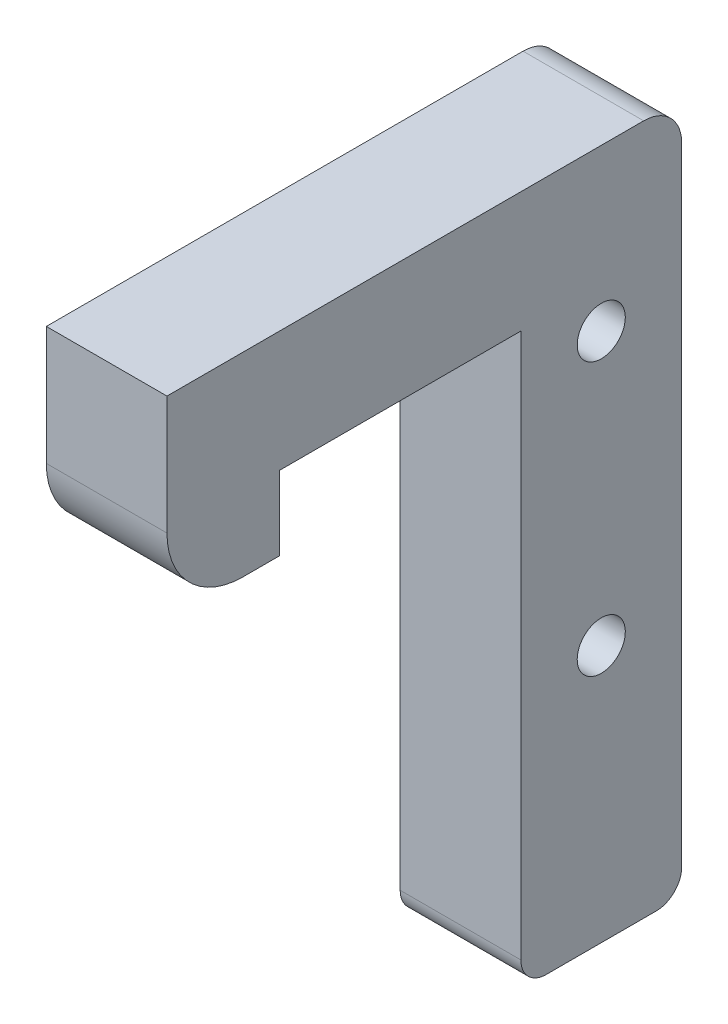
SolidWorks part; units mm, degrees
ref_plane "정면" through (0, 0, 0) normal (0, 0, 1) x (1, 0, 0)
ref_plane "윗면" through (0, 0, 0) normal (0, 1, 0) x (1, 0, 0)
ref_plane "우측면" through (0, 0, 0) normal (1, 0, 0) x (0, 0, -1)
sketch "Sketch1" plane through (0, 0, 0) normal (0, 0, 1) x (1, 0, 0)
  line L1 (0, 0) -> (-9.525, 0)
  line L2 (0, 0) -> (0, 9.525)
  line L3 (0, 9.525) -> (-9.525, 9.525)
  line L4 (-9.525, 0) -> (-9.525, 9.525)
  dimension "D1" = 9.525
  dimension "D2" = 9.525
extrude "Extrude1" add sketch "Sketch1" along normal blind 40.64
ref_plane "Plane1" through (-9.525, 0, 40.64) normal (0, 0, -1) x (-1, 0, 0)
sketch "Sketch3" plane through (0, 0, 0) normal (0, -1, 0) x (1, 0, 0)
  line L0 (0, 40.64) -> (0, 0) construction
  line L1 (-9.525, 40.64) -> (0, 40.64)
  line L2 (-9.525, 40.64) -> (-9.525, 31.75)
  line L3 (-9.525, 31.75) -> (0, 31.75)
  line L4 (0, 40.64) -> (0, 31.75)
  dimension "D1" = 8.89
extrude "Extrude2" add sketch "Sketch3" along normal blind 5.842
fillet "Fillet1" radius 6 1 edges at (-4.7625, -5.842, 40.64)
sketch "Sketch4" plane through (0, 0, 0) normal (0, -1, 0) x (1, 0, 0)
  line L0 (-9.525, 31.75) -> (-9.525, 0) construction
  line L1 (0, 0) -> (-9.525, 0)
  line L2 (0, 0) -> (0, 12.7)
  line L3 (0, 12.7) -> (-9.525, 12.7)
  line L4 (-9.525, 0) -> (-9.525, 12.7)
  dimension "D1" = 12.7
extrude "Extrude3" add sketch "Sketch4" along normal blind 45
ref_plane "Plane2" through (0, 9.525, 0) normal (0, 1, 0) x (-1, 0, 0)
fillet "Fillet2" radius 3 1 edges at (-4.7625, 9.525, 0)
hole_wizard "#6 Clearance Hole1" positions "3DSketch1" profile "Sketch5" hole size "#6" standard "Ansi Inch"
sketch3d "3DSketch1"
  line L0 (0, 9.525, 40.64) -> (0, 9.525, 3) construction
  line L2 (0, -45, 0) -> (0, 6.525, 0) construction
  point P0 (0, -3.175, 6.35)
  dimension "D1" = 12.7
  dimension "D2" = 6.35
sketch "Sketch5" plane through (0, -3.175, 6.35) normal (0, 1, 0) x (0, 0, -1)
  line L0 (0, 0) -> (0, 11.0468)
  line L1 (0, 11.0468) -> (1.8986, 9.906)
  line L2 (1.8986, 9.906) -> (1.8986, 0)
  line L5 (1.8986, 0) -> (0, 0)
  line L10 (0, 11.0468) -> (-1.8987, 9.906) construction
  line L11 (0, -6.35) -> (0, 107.95) construction
  dimension "Hole Dia." = 3.7973
  dimension "Hole Depth" = 9.906
  dimension "Drill Angle" = 118
hole_wizard "#6 Clearance Hole3" positions "3DSketch2" profile "Sketch6" hole size "#6" standard "Ansi Inch"
sketch3d "3DSketch2"
  line L0 (0, -45, 0) -> (0, -45, 12.7) construction
  line L1 (0, -45, 12.7) -> (-9.525, -45, 12.7) construction
  point P0 (-4.7625, -45, 6.35)
  dimension "D1" = 4.7625
  dimension "D2" = 6.35
sketch "Sketch6" plane through (-4.7625, -45, 6.35) normal (1, 0, 0) x (0, 0, -1)
  line L0 (0, 0) -> (0, 26.0328)
  line L1 (0, 26.0328) -> (1.8986, 24.892)
  line L2 (1.8986, 24.892) -> (1.8986, 0)
  line L5 (1.8986, 0) -> (0, 0)
  line L10 (0, 26.0328) -> (-1.8987, 24.892) construction
  line L11 (0, -6.35) -> (0, 107.95) construction
  dimension "Hole Dia." = 3.7973
  dimension "Hole Depth" = 24.892
  dimension "Drill Angle" = 118
hole_wizard "#6 Clearance Hole4" positions "3DSketch3" profile "Sketch7" hole size "#6" standard "Ansi Inch"
sketch3d "3DSketch3"
  line L1 (-9.525, 6.525, 0) -> (-9.525, -45, 0) construction
  line L2 (-9.525, -45, 12.7) -> (-9.525, -45, 0) construction
  point P0 (-9.525, -24.68, 6.35)
  dimension "D1" = 20.32
  dimension "D2" = 6.35
sketch "Sketch7" plane through (-9.525, -24.68, 6.35) normal (0, 1, 0) x (0, 0, 1)
  line L0 (0, 0) -> (0, 31.1128)
  line L1 (0, 31.1128) -> (1.8986, 29.972)
  line L2 (1.8986, 29.972) -> (1.8986, 0)
  line L5 (1.8986, 0) -> (0, 0)
  line L10 (0, 31.1128) -> (-1.8987, 29.972) construction
  line L11 (0, -6.35) -> (0, 107.95) construction
  dimension "Hole Dia." = 3.7973
  dimension "Hole Depth" = 29.972
  dimension "Drill Angle" = 118
fillet "Fillet3" radius 2 2 edges at (-4.7625, -45, 0) (-4.7625, -45, 12.7)
